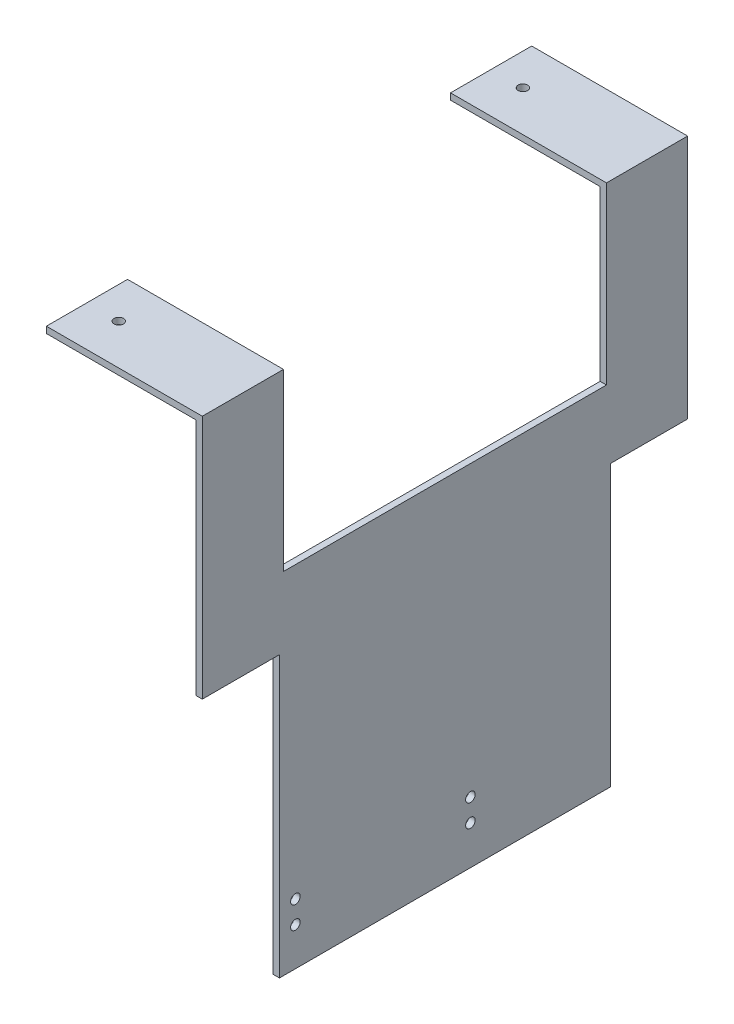
SolidWorks part; units mm, degrees
material "1060 Alloy"
ref_plane "Front Plane" through (0, 0, 0) normal (0, 0, 1) x (1, 0, 0)
ref_plane "Top Plane" through (0, 0, 0) normal (0, 1, 0) x (1, 0, 0)
ref_plane "Right Plane" through (0, 0, 0) normal (1, 0, 0) x (0, 0, -1)
sketch "Sketch2" plane through (0, 0, 0) normal (0, -1, 0) x (1, 0, 0)
  line L0 (441, -63.5) -> (451, -63.5) construction
  line L1 (441, -50.75) -> (490, -50.75)
  line L2 (441, -50.75) -> (441, -76.25)
  line L3 (441, -76.25) -> (490, -76.25)
  line L4 (490, -50.75) -> (490, -76.25)
  line L5 (451, -63.5) -> (451, 63.5) construction
  line L6 (451, 0) -> (481.6648, 0) construction
  line L7 (441, 76.25) -> (490, 76.25)
  line L8 (490, 50.75) -> (490, 76.25)
  line L9 (441, 50.75) -> (490, 50.75)
  line L10 (441, 50.75) -> (441, 76.25)
  circle A2 centre (451, 63.5) radius 1.5
  circle A3 centre (451, 63.5) radius 1.5
  circle A5 centre (451, -63.5) radius 1.5
  circle A6 centre (451, -63.5) radius 1.5
  dimension "D3" = 25.5
  dimension "D4" = 49
  dimension "D5" = 10
  dimension "D1" = 0
  dimension "D2" = 0
extrude "Boss-Extrude1" add sketch "Sketch2" along normal blind 2
sketch "Sketch3" plane through (0, -2, 0) normal (0, -1, 0) x (1, 0, 0)
  line L0 (441, 50.75) -> (490, 50.75) construction
  line L1 (490, 76.25) -> (488, 76.25)
  line L2 (490, 76.25) -> (490, 50.75)
  line L3 (490, 50.75) -> (488, 50.75)
  line L4 (488, 76.25) -> (488, 50.75)
  line L5 (441, -76.25) -> (490, -76.25) construction
  line L6 (490, -50.75) -> (488, -50.75)
  line L7 (490, -50.75) -> (490, -76.25)
  line L8 (490, -76.25) -> (488, -76.25)
  line L9 (488, -50.75) -> (488, -76.25)
  dimension "D1" = 2
  dimension "D2" = 2
extrude "Boss-Extrude2" add sketch "Sketch3" along normal blind 53
sketch "Sketch4" plane through (490, 0, 0) normal (1, 0, 0) x (0, 0, -1)
  line L0 (76.25, -55) -> (76.25, 0) construction
  line L1 (-76.25, -55) -> (76.25, -55)
  line L2 (-76.25, -55) -> (-76.25, -77)
  line L3 (-76.25, -77) -> (76.25, -77)
  line L4 (76.25, -55) -> (76.25, -77)
  line L5 (0, -165) -> (0, -1) construction
  line L6 (-52, -77) -> (52, -77)
  line L7 (-52, -77) -> (-52, -165)
  line L8 (-52, -165) -> (52, -165)
  line L9 (52, -77) -> (52, -165)
  line L10 (89, -1) -> (-89, -1) construction
  circle A0 centre (-47, -146) radius 1.5
  circle A1 centre (-47, -153) radius 1.5
  circle A2 centre (7.9995, -145.7713) radius 1.5
  circle A3 centre (8, -152.7713) radius 1.5
  line M13 (-76.25, -55) -> (-50.75, -55)
  dimension "D5" = 3
  dimension "D6" = 3
  dimension "D7" = 3
  dimension "D8" = 3
  dimension "D1" = 0
  dimension "D2" = 22
  dimension "D3" = 104
  dimension "D4" = 88
  dimension "D9" = 55
  dimension "D10" = 7
  dimension "D11" = 55
  dimension "D12" = 7
  dimension "D13" = 5
  dimension "D14" = 12
extrude "Boss-Extrude3" add sketch "Sketch4" against normal blind 2 contours L3 L5 L1 L2 M13 | L5 L6 L3 L4 L1 | L8 L5 L3 L7 A0 A1 | L5 L8 L9 L6 A3 A2
